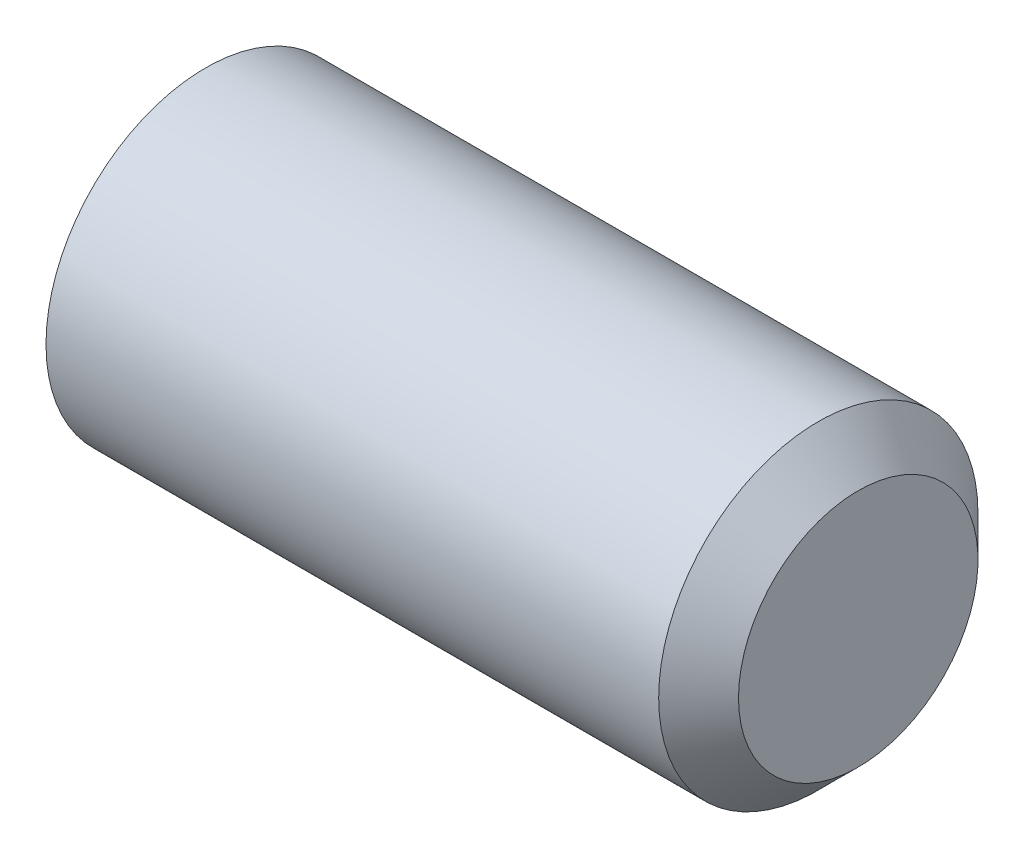
SolidWorks part; units mm, degrees
ref_plane "Plane1" through (0, 0, 0) normal (0, 0, 1) x (1, 0, 0)
ref_plane "Plane2" through (0, 0, 0) normal (0, 1, 0) x (1, 0, 0)
ref_plane "Plane3" through (0, 0, 0) normal (1, 0, 0) x (0, 0, -1)
sketch "BodySke" plane through (0, 0, 0) normal (0, 0, 1) x (1, 0, 0)
  line L0 (0, 0) -> (0, 10.352)
  line L1 (0, 10.352) -> (0.9515, 12)
  line L2 (0.9515, 12) -> (47, 12)
  line L3 (47, 12) -> (50, 9)
  line L4 (50, 0) -> (0, 0)
  line L5 (-12.7, 0) -> (88.9, 0) construction
  line L6 (50, 9) -> (50, 0)
  line L7 (50, 9) -> (50, 18.525) construction
  line L8 (0, -10.352) -> (0.9515, -12) construction
  line L9 (3, 15.875) -> (3, -3.175) construction
  line L10 (47, -12) -> (50, -9) construction
  dimension "Length" = 50
  dimension "Diameter" = 24
  dimension "Drive_ch_ang" = 60
  dimension "Minor_dia" = 20.704
  dimension "Cup_nose_ang" = 45
  dimension "Cup_dia" = 18
  dimension "Advance" = 3
revolve "BaseBody" add sketch "BodySke" angle 360 about L5
cosmetic thread "ThreadCosmetic" parameters "Thread_minor"=4.891
sketch "Sketch2" plane through (0, 0, 0) normal (-1, 0, 0) x (0, 0, 1)
  line L0 (3.4641, 6) -> (-3.4641, 6)
  line L1 (-3.4641, 6) -> (-6.9282, 0)
  line L2 (3.4641, 6) -> (6.9282, 0)
  line L3 (3.4641, -6) -> (6.9282, 0)
  line L4 (3.4641, -6) -> (-3.4641, -6)
  line L5 (-3.4641, -6) -> (-6.9282, 0)
  dimension "Hex_size" = 12
  dimension "D2" = 1.5
  dimension "D3" = 1.5
extrude "Hex" cut sketch "Sketch2" against normal blind 15
sketch "ThdSchSke" plane through (0, 0, 0) normal (0, 0, 1) x (1, 0, 0)
  line L0 (0.9515, -10.352) -> (-0.2025, -12)
  line L1 (0.9515, -10.352) -> (2.1054, -12)
  line L2 (2.1054, -12) -> (2.1054, -15)
  line L3 (-3.175, 0) -> (5.1513, 0) construction
  line L5 (2.1054, -15) -> (-0.2025, -15)
  line L6 (-0.2025, -15) -> (-0.2025, -12)
  line L8 (0.9515, 12) -> (0.9515, -12) construction
  dimension "Thread_minor" = 4.891
  dimension "Diameter" = 6
  dimension "SideAngle" = 55
  dimension "VeeAngle" = 70
  dimension "Overcut" = 7.5
revolve "ThreadSchematic" [suppressed] cut sketch "ThdSchSke" angle 360 about L3
pattern_linear "ThdSchPat" [suppressed]
equation "\"D2@Sketch2\" = \"Hex_size@Sketch2\" / 2"
equation "\"D3@Sketch2\" = \"Hex_size@Sketch2\" / 2"
equation "\"Thread_minor@ThreadCosmetic\" = \"Minor_dia@BodySke\""
equation "\"Thread_minor@ThdSchSke\" = \"Thread_minor@ThreadCosmetic\""
equation "\"Diameter@ThdSchSke\" = \"Diameter@BodySke\""
equation "\"Overcut@ThdSchSke\" = \"Diameter@BodySke\" * 1.25"
equation "\"Num_threads@ThdSchPat\" = int( (\"Length@BodySke\" - ( ( ( \"Diameter@BodySke\" - \"Minor_dia@BodySke\" ) * 0.5 ) / tan( \"Drive_ch_ang@BodySke\" * 0.017453292 ) ) - ( ( ( \"Diameter@BodySke\" - \"Cup_dia@BodySke\" ) * 0.5 ) * tan( \"Cup_nose_ang@BodySke\" * 0.017453292 ) ) ) / \"Advance@BodySke\" + 0.999 )  + 1"
equation "\"Advance@ThdSchPat\" = (\"Length@BodySke\" - ( ( ( \"Diameter@BodySke\" - \"Minor_dia@BodySke\" ) * 0.5 ) / tan( \"Drive_ch_ang@BodySke\" * 0.017453292 ) ) - ( ( ( \"Diameter@BodySke\" - \"Cup_dia@BodySke\" ) * 0.5 ) * tan( \"Cup_nose_ang@BodySke\" * 0.017453292 ) ) ) /  (\"Num_threads@ThdSchPat\" - 1) 'relax it"
equation "' \"Num_threads@ThdSchPat\" = \"Num_threads@ThdSchPat\" - sgn( \"Num_threads@ThdSchPat\" - 1) '---chamfered tips only---"
